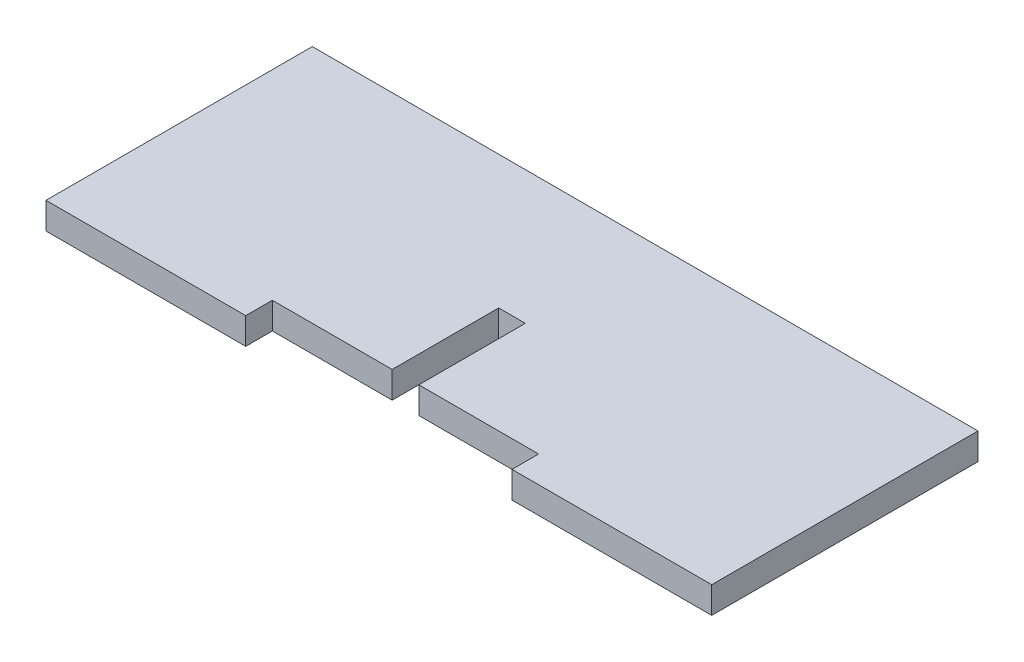
SolidWorks part; units mm, degrees
ref_plane "Plano frontal" through (0, 0, 0) normal (0, 0, 1) x (1, 0, 0)
ref_plane "Plano superior" through (0, 0, 0) normal (0, 1, 0) x (1, 0, 0)
ref_plane "Plano direito" through (0, 0, 0) normal (1, 0, 0) x (0, 0, -1)
sketch "Esboço1" plane through (0, 0, 0) normal (0, 1, 0) x (1, 0, 0)
  line L0 (-1.5, -22.6683) -> (-1.5, 7.3317) construction
  line L1 (-39, 7.3317) -> (36, 7.3317)
  line L2 (-39, 7.3317) -> (-39, -22.6683)
  line L3 (-39, -22.6683) -> (36, -22.6683)
  line L4 (36, 7.3317) -> (36, -22.6683)
  line L5 (-3, -22.6683) -> (-3, -7.6683)
  line L6 (-3, -7.6683) -> (0, -7.6683)
  line L7 (0, -7.6683) -> (0, -22.6683)
  point P11 (-1.5, -7.6683)
  dimension "D1" = 75
  dimension "D2" = 30
  dimension "D3" = 3
  dimension "D4" = 15
  dimension "D5" = 1.5
extrude "Ressalto-extrusão1" add sketch "Esboço1" along normal blind 3 contours L0 L3 L4 L1 | L3 L0 L1 L2 L5 L6 L7
sketch "Esboço2" plane through (0, 0, 22.6683) normal (0, 0, 1) x (1, 0, 0)
  line L0 (-39, 3) -> (-39, 0) construction
  line L1 (-16.5, 8.2807) -> (13.5, 8.2807)
  line L2 (-16.5, 8.2807) -> (-16.5, -7.862)
  line L3 (-16.5, -7.862) -> (13.5, -7.862)
  line L4 (13.5, 8.2807) -> (13.5, -7.862)
  point P6 (-39, 1.5)
  dimension "D1" = 30
  dimension "D2" = 22.5
extrude "Corte-extrusão2" cut sketch "Esboço2" against normal blind 3
